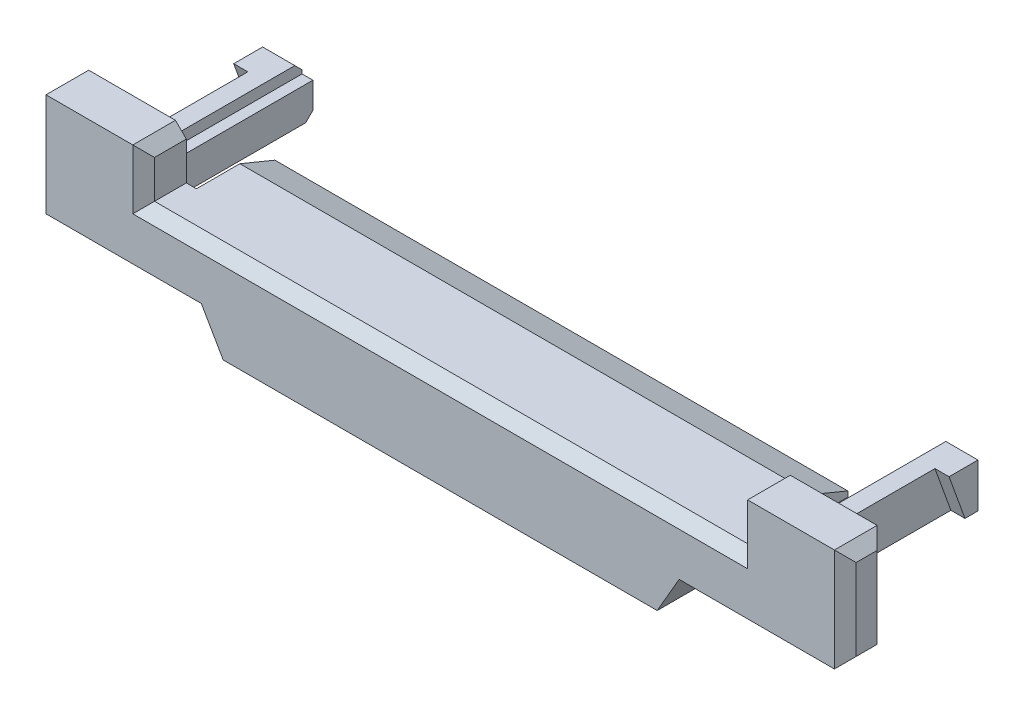
SolidWorks part; units mm, degrees
ref_plane "Płaszczyzna przednia" through (0, 0, 0) normal (0, 0, 1) x (1, 0, 0)
ref_plane "Płaszczyzna górna" through (0, 0, 0) normal (0, 1, 0) x (1, 0, 0)
ref_plane "Płaszczyzna prawa" through (0, 0, 0) normal (1, 0, 0) x (0, 0, -1)
sketch "Sketch1" plane through (0, 0, 0) normal (0, 0, 1) x (1, 0, 0)
  line L0 (-8.2, 0.6) -> (-8.2, 1.95)
  line L1 (-8.2, 1.95) -> (-11.2, 1.95)
  line L2 (-11.2, 1.95) -> (-11.2, -0.9)
  line L3 (-11.2, -0.9) -> (-6.6062, -0.9)
  line L4 (-6.6062, -0.9) -> (-6, -1.95)
  line L5 (-6, -1.95) -> (6, -1.95)
  line L6 (6, -1.95) -> (6.6062, -0.9)
  line L7 (6.6062, -0.9) -> (11.2, -0.9)
  line L8 (11.2, -0.9) -> (11.2, 1.95)
  line L9 (11.2, 1.95) -> (8.2, 1.95)
  line L10 (8.2, 1.95) -> (8.2, 0.6)
  line L11 (8.2, 0.6) -> (-8.2, 0.6)
extrude "Boss-Extrude1" add sketch "Sketch1" along normal blind 1.18
sketch "Sketch2" plane through (0, 0.6, 0) normal (0, 1, 0) x (1, 0, 0)
  line L0 (0, -1.18) -> (0, 2.17) construction
  line L1 (8.2, -1.18) -> (-8.2, -1.18) construction
  line L2 (7.92, 0) -> (7.92, 2.17)
  line L3 (8.2, 0) -> (-8.2, 0) construction
  line L4 (7.92, 2.17) -> (-7.92, 2.17)
  line L5 (-7.92, 2.17) -> (-7.92, 0)
  line L6 (8.2, -1.18) -> (8.2, 0) construction
  line L7 (7.92, 0) -> (-7.92, 0)
  dimension "D1" = 0.28
  dimension "D2" = 2.17
extrude "Boss-Extrude2" add sketch "Sketch2" against normal blind 0.55
sketch "Sketch3" plane through (-7.92, 0, 0) normal (-1, 0, 0) x (0, 0, 1)
  line L0 (-1.2, 0.6) -> (-2.17, 0.2)
  line L1 (-2.17, 0.6) -> (0, 0.6) construction
  line L2 (-2.17, 0.05) -> (-2.17, 0.6) construction
  line L3 (-2.17, 0.2) -> (-2.17, 0.6)
  line L4 (-2.17, 0.6) -> (-1.2, 0.6)
  dimension "D1" = 0.97
  dimension "D2" = 0.4
extrude "Cut-Extrude1" cut sketch "Sketch3" against normal through all both and the other way through all
chamfer "Chamfer1" distance 0.3 angle 45 8 edges at (11.2, -0.9, 0.59) (11.2, 0.525, 1.18) (11.2, 1.95, 0.59) (11.2, 0.525, 0) (-11.2, 1.95, 0.59) (-11.2, 0.525, 1.18) (-11.2, -0.9, 0.59) (-11.2, 0.525, 0)
chamfer "Chamfer2" distance 0.3 angle 45 5 edges at (-8.2, 1.95, 0.59) (-8.2, 1.275, 1.18) (8.2, 1.95, 0.59) (8.2, 1.275, 1.18) (0, 0.6, 1.18)
sketch "Sketch4" plane through (0, 0, 0) normal (0, 0, -1) x (-1, 0, 0)
  line L0 (-10.9, 1.95) -> (-8.5, 1.95) construction
  line L1 (-9.89, -0.11) -> (-8.7, -0.11)
  line L2 (-9.89, -0.11) -> (-9.89, 1.11)
  line L3 (-9.89, 1.11) -> (-8.7, 1.11)
  line L4 (-8.7, -0.11) -> (-8.7, 1.11)
  line L5 (-9.89, -0.11) -> (-8.7, 1.11) construction
  line L6 (-9.89, 1.11) -> (-8.7, -0.11) construction
  line L7 (-11.2, -0.6) -> (-11.2, 1.65) construction
  point P0 (-9.295, 0.5)
  dimension "D1" = 1.22
  dimension "D2" = 1.19
  dimension "D3" = 0.84
  dimension "D4" = 1.31
extrude "Boss-Extrude3" add sketch "Sketch4" along normal blind 4 separate body
sketch "Sketch5" plane through (0, 0, -4) normal (0, 0, -1) x (-1, 0, 0)
  line L0 (-9, 1.11) -> (-9, 0.81)
  line L1 (-8.7, 1.11) -> (-9.89, 1.11) construction
  line L2 (-9, 0.81) -> (-8.7, 0.81)
  line L3 (-8.7, -0.11) -> (-8.7, 1.11) construction
  line L4 (-8.7, 0.81) -> (-8.7, 1.11)
  line L5 (-8.7, 1.11) -> (-9, 1.11)
  dimension "D1" = 0.3
  dimension "D2" = 0.3
extrude "Cut-Extrude2" cut sketch "Sketch5" against normal up to surface (4 mm away) up to face at (0, 0.3389, 0)
chamfer "Chamfer3" distance 0.2 angle 45 3 edges at (9.295, -0.11, -4) (9.89, 0.5, -4) (9.445, 1.11, -4)
sketch "Sketch6" plane through (9.89, 0, 0) normal (1, 0, 0) x (0, 0, -1)
  line L0 (0, -0.11) -> (3.44, -0.11) construction
  line L1 (3.8, -0.11) -> (0, -0.11) construction
  line L2 (0, 1.11) -> (3, 1.11) construction
  line L3 (3.8, 1.11) -> (0, 1.11) construction
  line L4 (3.44, -0.11) -> (3, 1.11)
  line L5 (3.44, -0.11) -> (0, -0.11)
  line L6 (0, -0.11) -> (0, 1.11)
  line L7 (0, 1.11) -> (3, 1.11)
extrude "Cut-Extrude3" cut sketch "Sketch6" against normal blind 0.39
ref_plane "Plane1" through (0, 0, 0) normal (1, 0, 0) x (0, 0, -1)
mirror "Mirror1" about plane through (0, 0, 0) normal (1, 0, 0) of bodies 106
